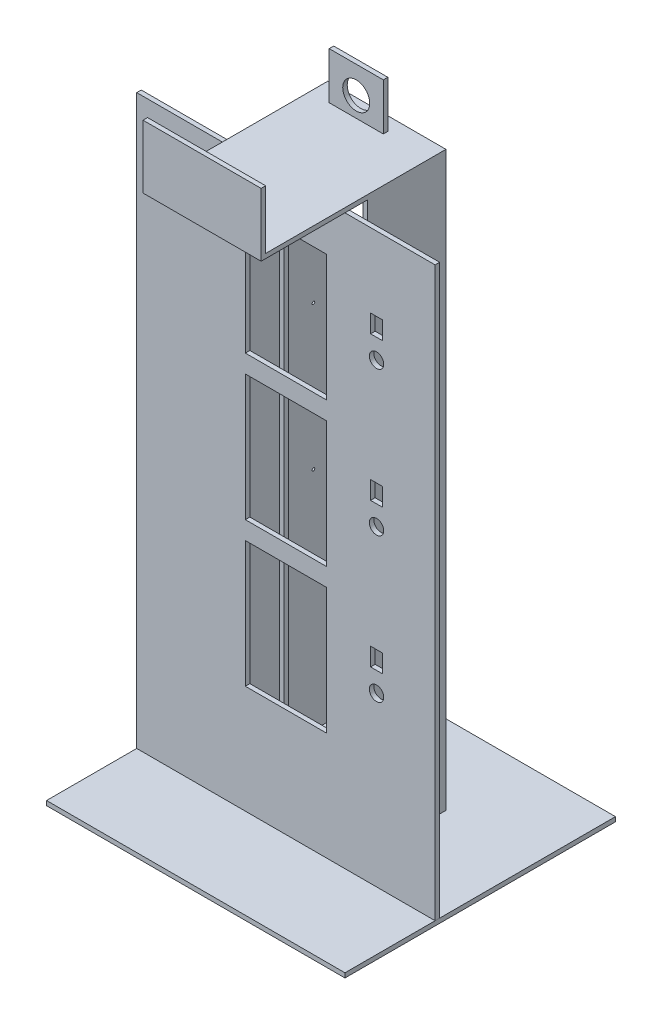
SolidWorks part; units mm, degrees
ref_plane "Plan de face" through (0, 0, 0) normal (0, 0, 1) x (1, 0, 0)
ref_plane "Plan de dessus" through (0, 0, 0) normal (0, 1, 0) x (1, 0, 0)
ref_plane "Plan de droite" through (0, 0, 0) normal (1, 0, 0) x (0, 0, -1)
sketch "Esquisse1" plane through (0, 0, 0) normal (1, 0, 0) x (0, 0, -1)
  line L1 (0, 0) -> (102, 0)
  line L2 (0, 0) -> (0, 630)
  line L3 (0, 630) -> (102, 630)
  line L4 (102, 0) -> (102, 630)
  dimension "D1" = 102
  dimension "D2" = 630
extrude "Boss.-Extru.1" add sketch "Esquisse1" along normal blind 131
sketch "Esquisse2" plane through (0, 0, 0) normal (0, 0, 1) x (1, 0, 0)
  line L0 (131, 0) -> (0, 0) construction
  line L5 (5, 0) -> (126, 0)
  line L7 (5, 0) -> (5, 630)
  line L8 (5, 630) -> (126, 630)
  line L9 (126, 0) -> (126, 630)
  line L10 (131, 630) -> (0, 630) construction
  line L11 (0, 630) -> (0, 0) construction
  dimension "D1" = 121
  dimension "D2" = 5
extrude "Enlèv. mat.-Extru.1" cut sketch "Esquisse2" against normal through all
sketch "Esquisse3" plane through (5, 0, 0) normal (1, 0, 0) x (0, 0, -1)
  line L0 (0, 0) -> (102, 0) construction
  line L1 (48.5, 0) -> (53.5, 0)
  line L2 (48.5, 0) -> (48.5, 630)
  line L3 (48.5, 630) -> (53.5, 630)
  line L4 (53.5, 0) -> (53.5, 630)
  line L5 (102, 630) -> (0, 630) construction
  line L6 (0, 630) -> (0, 0) construction
  dimension "D1" = 5
  dimension "D2" = 48.5
extrude "Boss.-Extru.2" add sketch "Esquisse3" along normal blind 5
sketch "Esquisse4" plane through (126, 0, 0) normal (-1, 0, 0) x (0, 0, 1)
  line L0 (0, 0) -> (-102, 0) construction
  line L1 (-53.5, 0) -> (-48.5, 0)
  line L2 (-53.5, 0) -> (-53.5, 630)
  line L3 (-53.5, 630) -> (-48.5, 630)
  line L4 (-48.5, 0) -> (-48.5, 630)
  line L5 (-102, 630) -> (0, 630) construction
  line L6 (-102, 0) -> (-102, 630) construction
  dimension "D1" = 5
  dimension "D2" = 48.5
extrude "Boss.-Extru.3" add sketch "Esquisse4" along normal blind 5
sketch "Esquisse5" plane through (0, 0, 0) normal (0, 0, 1) x (1, 0, 0)
  line L1 (-100, 0) -> (231, 0)
  line L2 (-100, 0) -> (-100, 630)
  line L3 (-100, 630) -> (231, 630)
  line L4 (231, 0) -> (231, 630)
  line L6 (0, 630) -> (0, 0) construction
  line L9 (5, 630) -> (0, 630) construction
  dimension "D1" = 630
  dimension "D2" = 331
  dimension "D3" = 100
  dimension "D4" = 0
extrude "Boss.-Extru.4" add sketch "Esquisse5" along normal blind 5
sketch "Esquisse6" plane through (0, 0, 0) normal (0, 0, -1) x (-1, 0, 0)
  line L0 (-121, 630) -> (-121, 0) construction
  line L1 (-110.5, 120) -> (-20.5, 120)
  line L2 (-110.5, 120) -> (-110.5, 260)
  line L3 (-110.5, 260) -> (-20.5, 260)
  line L4 (-20.5, 120) -> (-20.5, 260)
  line L10 (-5, 0) -> (-126, 0) construction
  line L12 (-110.5, 280) -> (-20.5, 280)
  line L13 (-110.5, 280) -> (-110.5, 420)
  line L14 (-110.5, 420) -> (-20.5, 420)
  line L15 (-20.5, 280) -> (-20.5, 420)
  line L16 (-110.5, 440) -> (-20.5, 440)
  line L17 (-110.5, 440) -> (-110.5, 580)
  line L18 (-110.5, 580) -> (-20.5, 580)
  line L19 (-20.5, 440) -> (-20.5, 580)
  dimension "D1" = 140
  dimension "D2" = 90
  dimension "D3" = 10.5
  dimension "D4" = 120
  dimension "D5" = 140
  dimension "D6" = 90
  dimension "D7" = 20
  dimension "D8" = 10.5
  dimension "D9" = 90
  dimension "D10" = 20
  dimension "D11" = 140
  dimension "D12" = 10.5
extrude "Enlèv. mat.-Extru.2" cut sketch "Esquisse6" against normal through all
sketch "Esquisse7" plane through (0, 0, 5) normal (0, 0, 1) x (1, 0, 0)
  line L2 (110.5, 120) -> (20.5, 120) construction
  line L3 (110.5, 260) -> (110.5, 120) construction
  line L4 (110.5, 280) -> (20.5, 280) construction
  line L5 (110.5, 420) -> (110.5, 280) construction
  line L6 (110.5, 440) -> (20.5, 440) construction
  line L7 (110.5, 580) -> (110.5, 440) construction
  line L9 (159.4, 208) -> (172.6, 208)
  line L10 (159.4, 208) -> (159.4, 228)
  line L11 (159.4, 228) -> (172.6, 228)
  line L12 (172.6, 208) -> (172.6, 228)
  line L13 (159.4, 368) -> (172.6, 368)
  line L14 (159.4, 368) -> (159.4, 388)
  line L15 (159.4, 388) -> (172.6, 388)
  line L16 (172.6, 368) -> (172.6, 388)
  line L17 (159.4, 528) -> (172.6, 528)
  line L18 (159.4, 528) -> (159.4, 548)
  line L19 (159.4, 548) -> (172.6, 548)
  line L20 (172.6, 528) -> (172.6, 548)
  circle A0 centre (166, 186) radius 8
  circle A1 centre (166, 346) radius 8
  circle A2 centre (166, 506) radius 8
  dimension "D1" = 16
  dimension "D2" = 66
  dimension "D4" = 16
  dimension "D5" = 66
  dimension "D7" = 16
  dimension "D9" = 55.5
  dimension "D3" = 55.5
  dimension "D6" = 55.5
  dimension "D8" = 66
  dimension "D10" = 20
  dimension "D11" = 13.2
  dimension "D12" = 6.6
  dimension "D13" = 88
  dimension "D14" = 13.2
  dimension "D15" = 20
  dimension "D16" = 6.6
  dimension "D17" = 88
  dimension "D18" = 20
  dimension "D19" = 13.2
  dimension "D20" = 6.6
  dimension "D21" = 88
extrude "Enlèv. mat.-Extru.3" cut sketch "Esquisse7" against normal through all
sketch "Esquisse8" plane through (0, 0, 0) normal (-1, 0, 0) x (0, 0, 1)
  line L1 (0, 0) -> (-20, 0)
  line L2 (0, 0) -> (0, 20)
  line L3 (0, 20) -> (-20, 20)
  line L4 (-20, 0) -> (-20, 20)
  dimension "D1" = 20
  dimension "D2" = 20
extrude "Enlèv. mat.-Extru.4" cut sketch "Esquisse8" against normal through all
sketch "Esquisse9" plane through (0, 0, -102) normal (0, 0, -1) x (-1, 0, 0)
  line L1 (-131, 0) -> (0, 0)
  line L2 (-131, 0) -> (-131, 630)
  line L3 (-131, 630) -> (0, 630)
  line L4 (0, 0) -> (0, 630)
extrude "Boss.-Extru.5" add sketch "Esquisse9" along normal blind 5
sketch "Esquisse10" plane through (0, 0, -107) normal (0, 0, -1) x (-1, 0, 0)
  line L0 (-131, 0) -> (0, 0) construction
  line L1 (-111, 75) -> (-20, 75)
  line L2 (-111, 75) -> (-111, 615)
  line L3 (-111, 615) -> (-20, 615)
  line L4 (-20, 75) -> (-20, 615)
  line L5 (-131, 630) -> (-131, 0) construction
  line L6 (0, 0) -> (0, 630) construction
  line L7 (0, 630) -> (-131, 630) construction
  dimension "D1" = 75
  dimension "D2" = 20
  dimension "D3" = 20
  dimension "D4" = 15
extrude "Enlèv. mat.-Extru.5" cut sketch "Esquisse10" against normal blind 5
sketch "Esquisse11" plane through (0, 0, -107) normal (0, 0, -1) x (-1, 0, 0)
  line L0 (-131, 0) -> (0, 0) construction
  line L1 (-111, 60) -> (-20, 60)
  line L2 (-111, 60) -> (-111, 0)
  line L3 (-111, 0) -> (-20, 0)
  line L4 (-20, 60) -> (-20, 0)
  line L5 (-111, 75) -> (-20, 75) construction
  dimension "D1" = 15
extrude "Enlèv. mat.-Extru.6" cut sketch "Esquisse11" against normal blind 5
sketch "Esquisse12" plane through (0, 0, -102) normal (0, 0, 1) x (1, 0, 0)
  line L0 (111, 75) -> (20, 75) construction
  line L1 (55.5, 75) -> (75.5, 75)
  line L2 (55.5, 75) -> (55.5, 70)
  line L3 (55.5, 70) -> (75.5, 70)
  line L4 (75.5, 75) -> (75.5, 70)
  line L5 (20, 75) -> (20, 615) construction
  dimension "D1" = 35.5
  dimension "D2" = 20
  dimension "D3" = 5
extrude "Boss.-Extru.6" add sketch "Esquisse12" along normal through all
sketch "Esquisse13" plane through (0, 0, 5) normal (0, 0, 1) x (1, 0, 0)
  line L1 (-100, 0) -> (231, 0)
  line L2 (-100, 0) -> (-100, -5)
  line L3 (-100, -5) -> (231, -5)
  line L4 (231, 0) -> (231, -5)
  dimension "D1" = 5
extrude "Boss.-Extru.7" add sketch "Esquisse13" along normal blind 100 and the other way blind 200 separate body
sketch "Esquisse15" plane through (0, 0, -107) normal (0, 0, -1) x (-1, 0, 0)
  line L1 (-131, 630) -> (0, 630)
  line L2 (-131, 630) -> (-131, 635)
  line L3 (-131, 635) -> (0, 635)
  line L4 (0, 630) -> (0, 635)
  dimension "D1" = 5
extrude "Boss.-Extru.8" add sketch "Esquisse15" against normal blind 200
sketch "Esquisse16" plane through (131, 0, 0) normal (1, 0, 0) x (0, 0, -1)
  line L1 (0, 630) -> (20, 630)
  line L2 (0, 630) -> (0, 610)
  line L3 (0, 610) -> (20, 610)
  line L4 (20, 630) -> (20, 610)
  dimension "D1" = 20
  dimension "D2" = 20
extrude "Enlèv. mat.-Extru.7" cut sketch "Esquisse16" against normal through all
sketch "Esquisse18" plane through (5, 0, 0) normal (1, 0, 0) x (0, 0, -1)
  line L13 (102, 630) -> (102, 0) construction
  circle A0 centre (86, 595) radius 1.5
  circle A1 centre (86, 435) radius 1.5
  circle A2 centre (86, 275) radius 1.5
  dimension "D3" = 3
  dimension "D6" = 3
  dimension "D9" = 3
  dimension "D1" = 16
  dimension "D2" = 15
  dimension "D4" = 16
  dimension "D5" = 15
  dimension "D7" = 16
  dimension "D8" = 15
extrude "Enlèv. mat.-Extru.8" cut sketch "Esquisse18" against normal through all
sketch "Esquisse19" plane through (0, 635, 0) normal (0, 1, 0) x (1, 0, 0)
  line L0 (65.5, 107) -> (65.5, 82)
  line L1 (0, 107) -> (131, 107) construction
  dimension "D1" = 25
ref_plane "Plan1" through (0, 0, -87) normal (0, 0, -1) x (-1, 0, 0)
sketch "Esquisse21" plane through (0, 0, -87) normal (0, 0, -1) x (-1, 0, 0)
  line L0 (0, 635) -> (-131, 635) construction
  line L1 (-81.5, 635) -> (-21.5, 635)
  line L2 (-81.5, 635) -> (-81.5, 687)
  line L3 (-81.5, 687) -> (-21.5, 687)
  line L4 (-21.5, 635) -> (-21.5, 687)
  line L6 (-131, 635) -> (-131, 0) construction
  circle A0 centre (-51.5, 657) radius 15
  dimension "D3" = 30
  dimension "D1" = 52
  dimension "D2" = 60
  dimension "D4" = 22
  dimension "D5" = 30
  dimension "D6" = 79.5
extrude "Boss.-Extru.9" add sketch "Esquisse21" along normal blind 5
sketch "Esquisse22" plane through (0, 630, 0) normal (0, -1, 0) x (1, 0, 0)
  line L1 (0, 93) -> (131, 93)
  line L2 (0, 93) -> (0, 98)
  line L3 (0, 98) -> (131, 98)
  line L4 (131, 93) -> (131, 98)
  dimension "D1" = 5
  dimension "D2" = 131
extrude "Boss.-Extru.10" add sketch "Esquisse22" against normal blind 70
